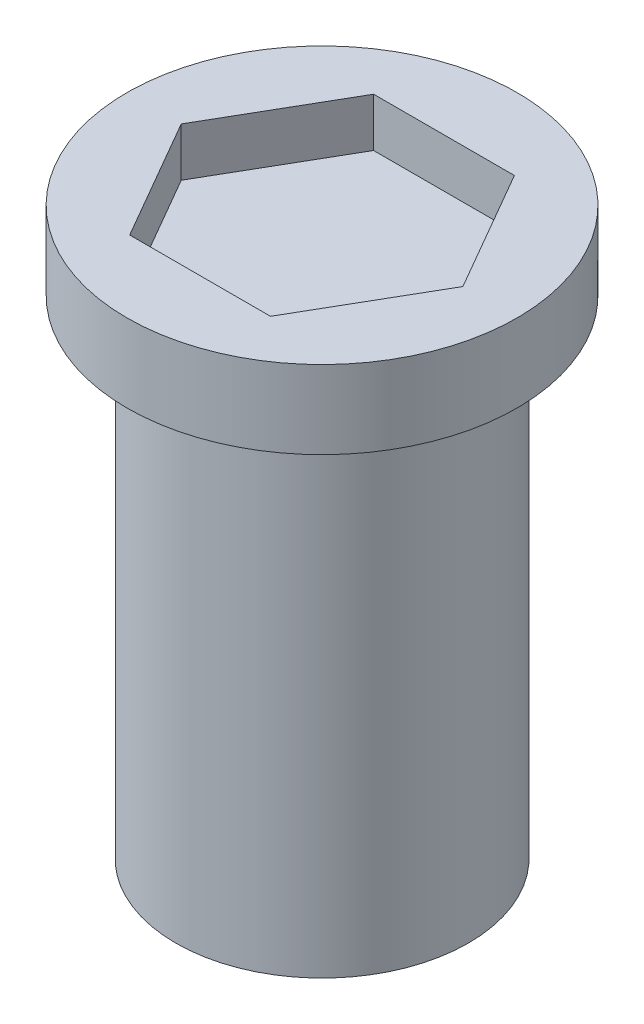
SolidWorks part; units mm, degrees
ref_plane "Front Plane" through (0, 0, 0) normal (0, 0, 1) x (1, 0, 0)
ref_plane "Top Plane" through (0, 0, 0) normal (0, 1, 0) x (1, 0, 0)
ref_plane "Right Plane" through (0, 0, 0) normal (1, 0, 0) x (0, 0, -1)
sketch "Sketch1" plane through (0, 0, 0) normal (0, 1, 0) x (1, 0, 0)
  circle A0 centre (0, 0) radius 15
  dimension "D1" = 30
extrude "Boss-Extrude1" add sketch "Sketch1" along normal blind 50
sketch "Sketch2" plane through (0, 50, 0) normal (0, 1, 0) x (1, 0, 0)
  circle A0 centre (0, 0) radius 20
  dimension "D1" = 40
extrude "Boss-Extrude2" add sketch "Sketch2" along normal blind 8
sketch "Sketch3" plane through (0, 58, 0) normal (0, 1, 0) x (1, 0, 0)
  line L1 (-14.4338, 0) -> (-7.2169, -12.5)
  line L2 (-7.2169, -12.5) -> (7.2169, -12.5)
  line L3 (7.2169, -12.5) -> (14.4338, 0)
  line L4 (14.4338, 0) -> (7.2169, 12.5)
  line L5 (7.2169, 12.5) -> (-7.2169, 12.5)
  line L6 (-7.2169, 12.5) -> (-14.4338, 0)
  circle A0 centre (0, 0) radius 12.5 construction
  point P1 (0, 12.5)
  dimension "D1" = 25
extrude "Cut-Extrude1" cut sketch "Sketch3" against normal blind 5
